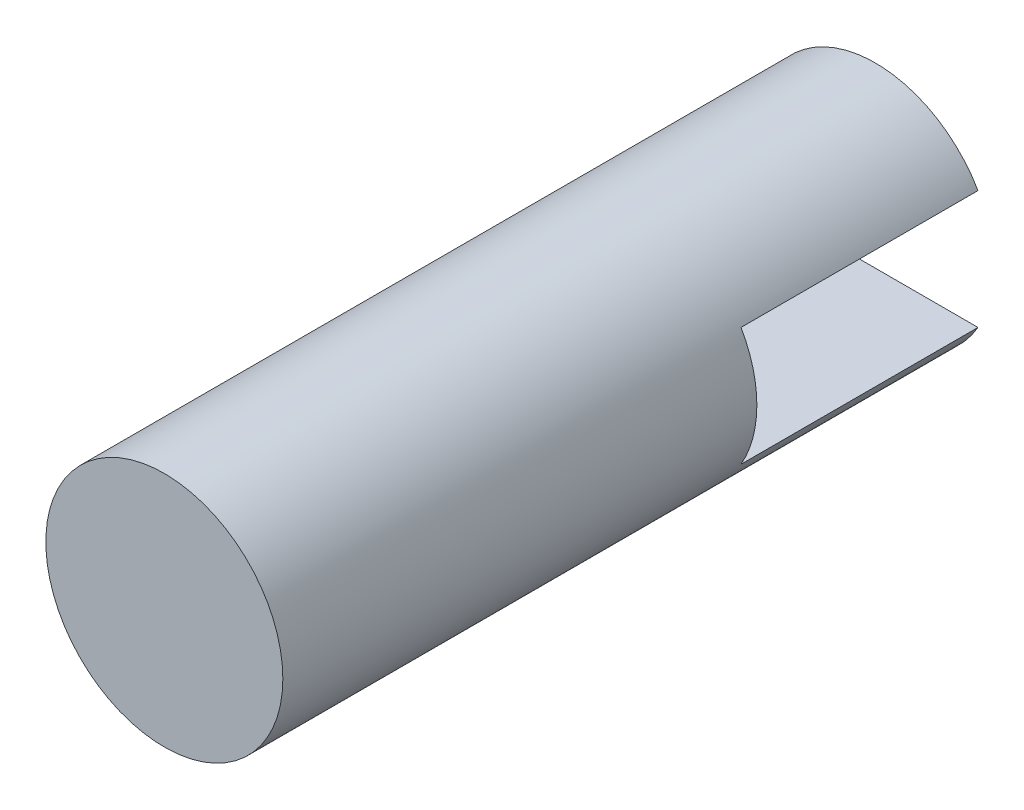
SolidWorks part; units mm, degrees
ref_plane "Front Plane" through (0, 0, 0) normal (0, 0, 1) x (1, 0, 0)
ref_plane "Top Plane" through (0, 0, 0) normal (0, 1, 0) x (1, 0, 0)
ref_plane "Right Plane" through (0, 0, 0) normal (1, 0, 0) x (0, 0, -1)
sketch "Sketch1" plane through (0, 0, 0) normal (0, 0, 1) x (1, 0, 0)
  circle A0 centre (0, 0) radius 5
  dimension "D1" = 10
extrude "Boss-Extrude1" add sketch "Sketch1" along normal blind 25 and the other way blind 5
sketch "Sketch3" plane through (0, 0, 0) normal (1, 0, 0) x (0, 0, -1)
  line L0 (5, -5) -> (5, 5) construction
  line L1 (5, -2.5) -> (-5, -2.5)
  line L2 (5, -2.5) -> (5, 2.5)
  line L3 (5, 2.5) -> (-5, 2.5)
  line L4 (-5, -2.5) -> (-5, 2.5)
  point P6 (0, -10.4655)
  point P7 (5, 0)
  point P9 (5, -10.7212)
  dimension "D1" = 5
  dimension "D2" = 10
extrude "Cut-Extrude2" cut sketch "Sketch3" against normal through all both and the other way through all
